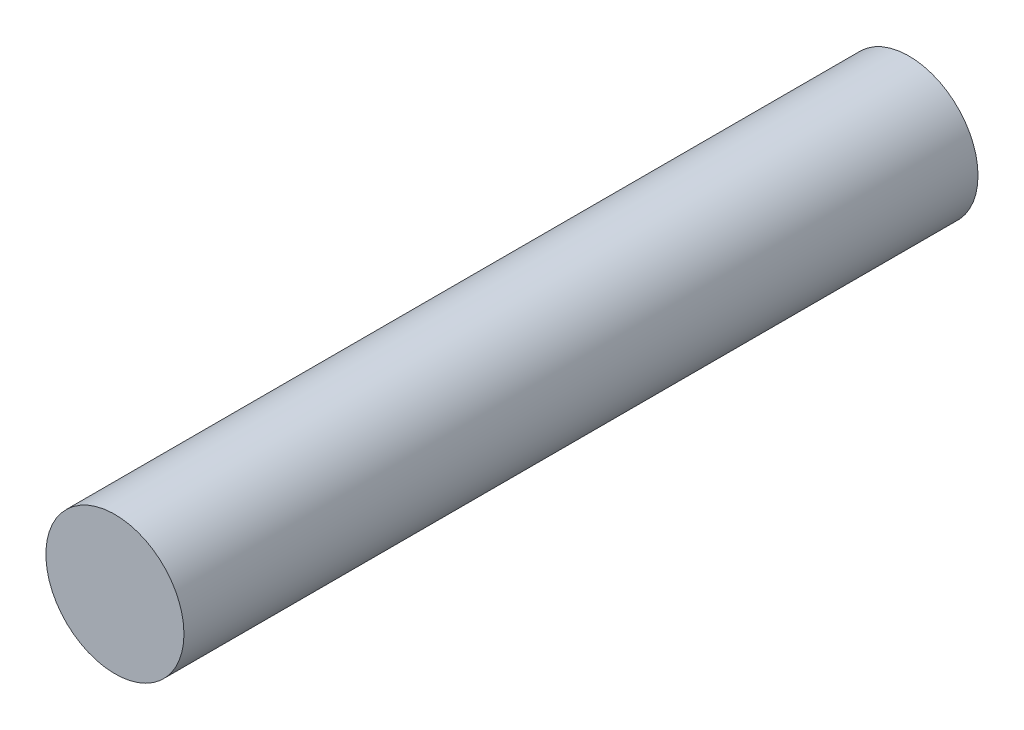
SolidWorks part; units mm, degrees
ref_plane "Front Plane" through (0, 0, 0) normal (0, 0, 1) x (1, 0, 0)
ref_plane "Top Plane" through (0, 0, 0) normal (0, 1, 0) x (1, 0, 0)
ref_plane "Right Plane" through (0, 0, 0) normal (1, 0, 0) x (0, 0, -1)
sketch "Sketch1" plane through (0, 0, 0) normal (0, 0, 1) x (1, 0, 0)
  circle A0 centre (0, 0) radius 10
  dimension "D1" = 20
extrude "Boss-Extrude1" add sketch "Sketch1" along normal blind 115
sketch "Sketch2" plane through (0, 0, 0) normal (0, 0, -1) x (-1, 0, 0)
  circle A0 centre (0, 0) radius 15.0994
sketch "Sketch3" plane through (0, 0, 0) normal (0, 0, -1) x (-1, 0, 0)
  circle A0 centre (0, 0) radius 5.08
extrude "Cut-Extrude1" cut sketch "Sketch3" against normal blind 2.54
